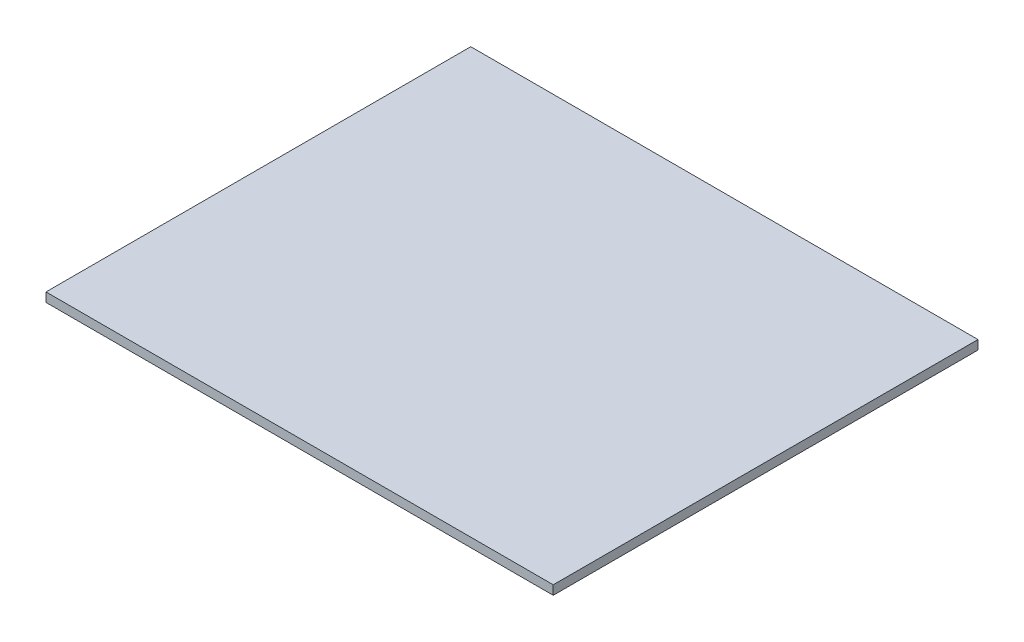
SolidWorks part; units mm, degrees
ref_plane "Front Plane" through (0, 0, 0) normal (0, 0, 1) x (1, 0, 0)
ref_plane "Top Plane" through (0, 0, 0) normal (0, 1, 0) x (1, 0, 0)
ref_plane "Right Plane" through (0, 0, 0) normal (1, 0, 0) x (0, 0, -1)
sketch "Sketch1" plane through (0, 0, 0) normal (0, 1, 0) x (1, 0, 0)
  line L1 (0, 0) -> (111.0988, 0)
  line L2 (0, 0) -> (0, 93.0339)
  line L3 (0, 93.0339) -> (111.0988, 93.0339)
  line L4 (111.0988, 0) -> (111.0988, 93.0339)
extrude "Boss-Extrude1" add sketch "Sketch1" along normal blind 2
